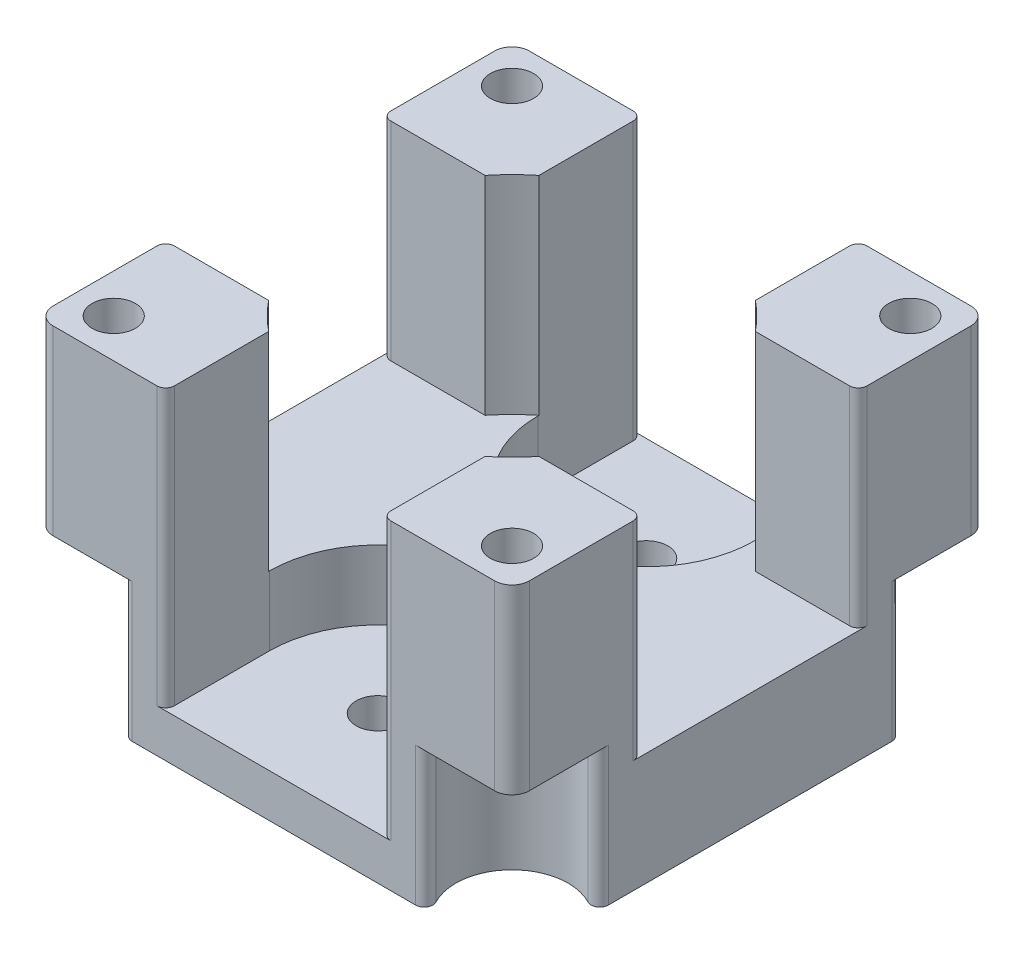
SolidWorks part; units mm, degrees
ref_plane "Front Plane" through (0, 0, 0) normal (0, 0, 1) x (1, 0, 0)
ref_plane "Top Plane" through (0, 0, 0) normal (0, 1, 0) x (1, 0, 0)
ref_plane "Right Plane" through (0, 0, 0) normal (1, 0, 0) x (0, 0, -1)
sketch "Sketch1" plane through (0, 0, 0) normal (0, 1, 0) x (1, 0, 0)
  line L1 (0, 0) -> (55, 0)
  line L2 (0, 0) -> (0, 55)
  line L3 (0, 55) -> (55, 55)
  line L4 (55, 0) -> (55, 55)
  dimension "D1" = 55
  dimension "D2" = 55
extrude "Boss-Extrude1" add sketch "Sketch1" along normal blind 37
sketch "Sketch2" plane through (0, 37, 0) normal (0, 1, 0) x (1, 0, 0)
  line L2 (0, 0) -> (55, 0) construction
  circle A0 centre (27.5, 27.5) radius 20
  dimension "D1" = 40
  dimension "D2" = 27.5
  dimension "D3" = 27.5
extrude "Cut-Extrude1" cut sketch "Sketch2" against normal blind 24
sketch "Sketch3" plane through (0, 37, 0) normal (0, 1, 0) x (1, 0, 0)
  line L0 (55, 55) -> (0, 55) construction
  line L1 (15, 55) -> (40, 55)
  line L2 (15, 55) -> (15, 0)
  line L3 (15, 0) -> (40, 0)
  line L4 (40, 55) -> (40, 0)
  line L5 (0, 0) -> (55, 0) construction
  line L6 (55, 0) -> (55, 55) construction
  line L7 (0, 55) -> (0, 0) construction
  dimension "D1" = 15
  dimension "D2" = 15
extrude "Cut-Extrude2" cut sketch "Sketch3" along direction (0, 1, 0) on the side against the normal blind 24
sketch "Sketch4" plane through (0, 37, 0) normal (0, 1, 0) x (1, 0, 0)
  line L0 (0, 55) -> (0, 0) construction
  line L1 (0, 40) -> (55, 40)
  line L2 (0, 40) -> (0, 15)
  line L3 (0, 15) -> (55, 15)
  line L4 (55, 40) -> (55, 15)
  line L5 (55, 0) -> (55, 55) construction
  line L6 (15, 55) -> (0, 55) construction
  line L7 (0, 0) -> (15, 0) construction
  dimension "D1" = 15
  dimension "D2" = 15
extrude "Cut-Extrude3" cut sketch "Sketch4" along direction (0, 1, 0) on the side against the normal blind 24
sketch "Sketch5" plane through (0, 37, 0) normal (0, 1, 0) x (1, 0, 0)
  line L0 (0, 0) -> (15, 0) construction
  line L1 (0, 15) -> (0, 0) construction
  circle A0 centre (4.5, 4.5) radius 2.5
  dimension "D1" = 5
  dimension "D2" = 4.5
  dimension "D3" = 4.5
extrude "Cut-Extrude4" cut sketch "Sketch5" against normal through all
sketch "Sketch6" plane through (0, 37, 0) normal (0, 1, 0) x (1, 0, 0)
  line L0 (55, 0) -> (55, 15) construction
  line L1 (40, 0) -> (55, 0) construction
  circle A0 centre (50.5, 4.5) radius 2.5
  dimension "D1" = 5
  dimension "D2" = 4.5
  dimension "D3" = 4.5
extrude "Cut-Extrude5" cut sketch "Sketch6" against normal through all
ref_plane "Plane1" through (0, 0, -27.5) normal (0, 0, -1) x (-1, 0, 0)
mirror "Mirror1" about plane through (0, 0, -27.5) normal (0, 0, -1) of "Cut-Extrude4", "Cut-Extrude5"
sketch "Sketch8" plane through (0, 0, 0) normal (0, -1, 0) x (1, 0, 0)
  circle A0 centre (50.5, -50.5) radius 6.5
  dimension "D1" = 13
extrude "Cut-Extrude6" cut sketch "Sketch8" against normal blind 16
sketch "Sketch15" plane through (0, 13, 0) normal (0, 1, 0) x (1, 0, 0)
  line L0 (40, 55) -> (15, 55) construction
  line L2 (0, 40) -> (0, 15) construction
  circle A0 centre (27.5, 43) radius 12.5
  spline S1 degree 1 poles (15, 55) (15, 43.1125) knots 0 0 1 1
  line M8 (40, 55) -> (15, 55)
  dimension "D1" = 25
  dimension "D2" = 12
  dimension "D3" = 27.5
extrude "Cut-Extrude11" cut sketch "Sketch15" against normal blind 8 contours A0 M8
sketch "Sketch16" plane through (0, 13, 0) normal (0, 1, 0) x (1, 0, 0)
  line L1 (15, 55) -> (40, 55)
  line L2 (15, 55) -> (15, 43)
  line L3 (15, 43) -> (40, 43)
  line L4 (40, 55) -> (40, 43)
  arc A0 (24, 55) -> (31, 55) centre (27.5, 43) ccw construction
extrude "Cut-Extrude12" cut sketch "Sketch16" along direction (0, 1, 0) on the side against the normal blind 8
mirror "Mirror2" about plane through (0, 0, -27.5) normal (0, 0, -1) of "Cut-Extrude2", "Cut-Extrude11"
sketch "Sketch17" plane through (0, 13, 0) normal (0, 1, 0) x (1, 0, 0)
  line L1 (15, 0) -> (40, 0)
  line L2 (15, 0) -> (15, 12)
  line L3 (15, 12) -> (40, 12)
  line L4 (40, 0) -> (40, 12)
  arc A0 (31, 0) -> (24, 0) centre (27.5, 12) ccw construction
extrude "Cut-Extrude13" cut sketch "Sketch17" along direction (0, 1, 0) on the side against the normal blind 8
sketch "Sketch18" plane through (0, 5, 0) normal (0, 1, 0) x (1, 0, 0)
  line L0 (40, 55) -> (15, 55) construction
  line L1 (0, 40) -> (0, 15) construction
  circle A0 centre (27.5, 43) radius 2.5
  dimension "D1" = 5
  dimension "D2" = 12
  dimension "D3" = 27.5
extrude "Cut-Extrude14" cut sketch "Sketch18" against normal through all
mirror "Mirror3" about plane through (0, 0, -27.5) normal (0, 0, -1) of "Cut-Extrude14"
ref_plane "Plane2" through (27.5, 0, 0) normal (1, 0, 0) x (0, 0, -1)
mirror "Mirror4" about plane through (27.5, 0, 0) normal (1, 0, 0) of "Cut-Extrude6"
mirror "Mirror5" about plane through (0, 0, -27.5) normal (0, 0, -1) of "Mirror4", "Cut-Extrude6"
fillet "Fillet2" radius 2 4 edges at (0, 26.5, 0) (55, 26.5, -55) (55, 26.5, 0) (0, 26.5, -55)
fillet "Fillet3" radius 1 8 edges at (9.1904, 8, 0) (0, 8, -9.1904) (45.8096, 8, 0) (55, 8, -9.1904) (0, 8, -45.8096) (9.1904, 8, -55) (55, 8, -45.8096) (45.8096, 8, -55)
fillet "Fillet4" radius 1 8 edges at (55, 25, -40) (40, 21, -55) (0, 25, -40) (15, 21, -55) (40, 21, 0) (55, 25, -15) (0, 25, -15) (15, 21, 0)
